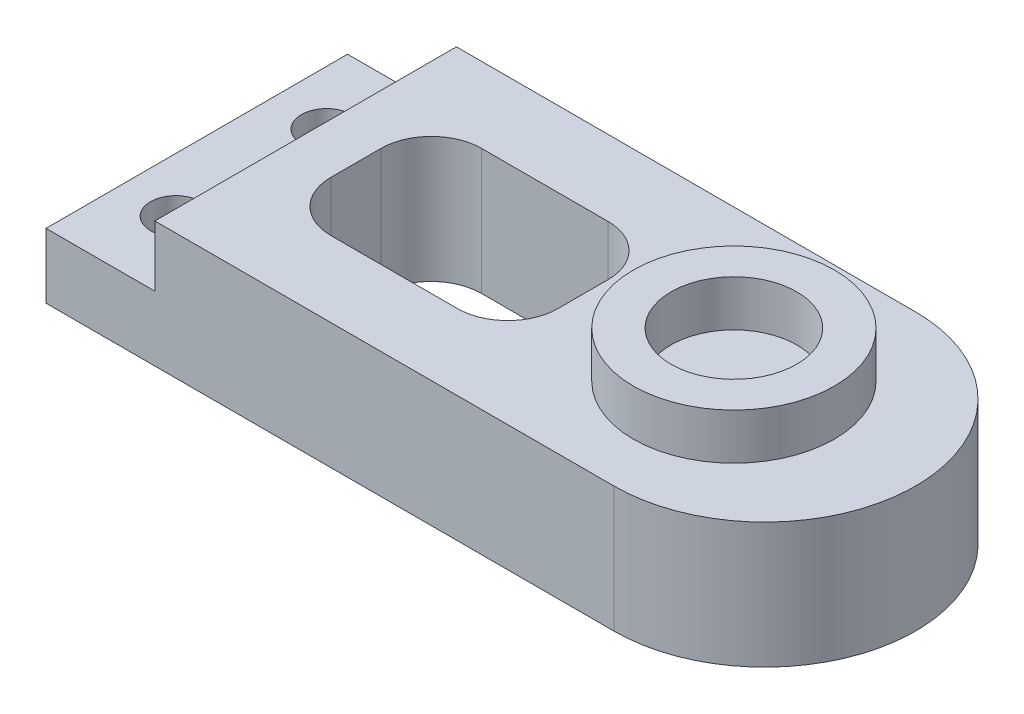
SolidWorks part; units mm, degrees
ref_plane "Front Plane" through (0, 0, 0) normal (0, 0, 1) x (1, 0, 0)
ref_plane "Top Plane" through (0, 0, 0) normal (0, 1, 0) x (1, 0, 0)
ref_plane "Right Plane" through (0, 0, 0) normal (1, 0, 0) x (0, 0, -1)
sketch "Sketch1" plane through (0, 0, 0) normal (0, 1, 0) x (1, 0, 0)
  line L5 (0, 0) -> (22.6, 0)
  line L6 (0, 0) -> (0, 12)
  line L7 (0, 12) -> (22.6, 12)
  arc A0 (22.6, 0) -> (22.6, 12) centre (22.6, 6) ccw
  dimension "D3" = 6
  dimension "D1" = 12
  dimension "D2" = 22.6
extrude "Boss-Extrude1" add sketch "Sketch1" along normal blind 5
sketch "Sketch2" plane through (0, 5, 0) normal (0, 1, 0) x (1, 0, 0)
  line L1 (0, 12) -> (4.33, 12)
  line L2 (0, 12) -> (0, 0)
  line L3 (0, 0) -> (4.33, 0)
  line L4 (4.33, 12) -> (4.33, 0)
  dimension "D1" = 4.33
  dimension "D2" = 12
extrude "Cut-Extrude1" cut sketch "Sketch2" against normal blind 2.42
sketch "Sketch3" plane through (0, 2.58, 0) normal (0, 1, 0) x (1, 0, 0)
  line L0 (0, 12) -> (0, 0) construction
  line L3 (0, 6) -> (4.33, 6) construction
  line L4 (4.33, 0) -> (4.33, 12) construction
  circle A0 centre (2.16, 9) radius 1
  circle A1 centre (2.16, 3) radius 1
  dimension "D1" = 2
  dimension "D2" = 6
  dimension "D4" = 2
  dimension "D5" = 2.16
extrude "Cut-Extrude2" cut sketch "Sketch3" against normal through all
sketch "Sketch5" plane through (0, 5, 0) normal (0, 1, 0) x (1, 0, 0)
  line L0 (22.6, 12) -> (4.33, 12) construction
  line L1 (0, 12) -> (0, 0) construction
  circle A0 centre (21.37, 6) radius 4
  circle A1 centre (21.37, 6) radius 2.5
  dimension "D1" = 8
  dimension "D2" = 5
  dimension "D3" = 6
  dimension "D4" = 21.37
extrude "Boss-Extrude2" add sketch "Sketch5" along normal blind 1.83
sketch "Sketch6" plane through (0, 5, 0) normal (0, 1, 0) x (1, 0, 0)
  line L0 (21.37, 6) -> (4.33, 6) construction
  line L1 (4.33, 0) -> (4.33, 12) construction
  line L2 (4.33, 0) -> (4.33, 12) construction
  line L3 (8.33, 9) -> (13.37, 9)
  line L4 (6.33, 7) -> (6.33, 5)
  line L5 (8.33, 3) -> (13.37, 3)
  line L6 (15.37, 7) -> (15.37, 5)
  line L7 (6.33, 9) -> (15.37, 3) construction
  line L8 (6.33, 3) -> (15.37, 9) construction
  line L9 (22.6, 12) -> (4.33, 12) construction
  circle A2 centre (21.37, 6) radius 4 construction
  arc A3 (15.37, 7) -> (13.37, 9) centre (13.37, 7) ccw
  arc A4 (15.37, 5) -> (13.37, 3) centre (13.37, 5) cw
  arc A5 (8.33, 3) -> (6.33, 5) centre (8.33, 5) cw
  arc A6 (8.33, 9) -> (6.33, 7) centre (8.33, 7) ccw
  point P5 (10.85, 6)
  dimension "D1" = 2
  dimension "D4" = 2
  dimension "D2" = 3
  dimension "D3" = 2
extrude "Cut-Extrude3" cut sketch "Sketch6" against normal through all
sketch "Sketch7" plane through (0, 2.58, 0) normal (0, 1, 0) x (1, 0, 0)
  line L0 (2.16, 9) -> (2.16, 3)
